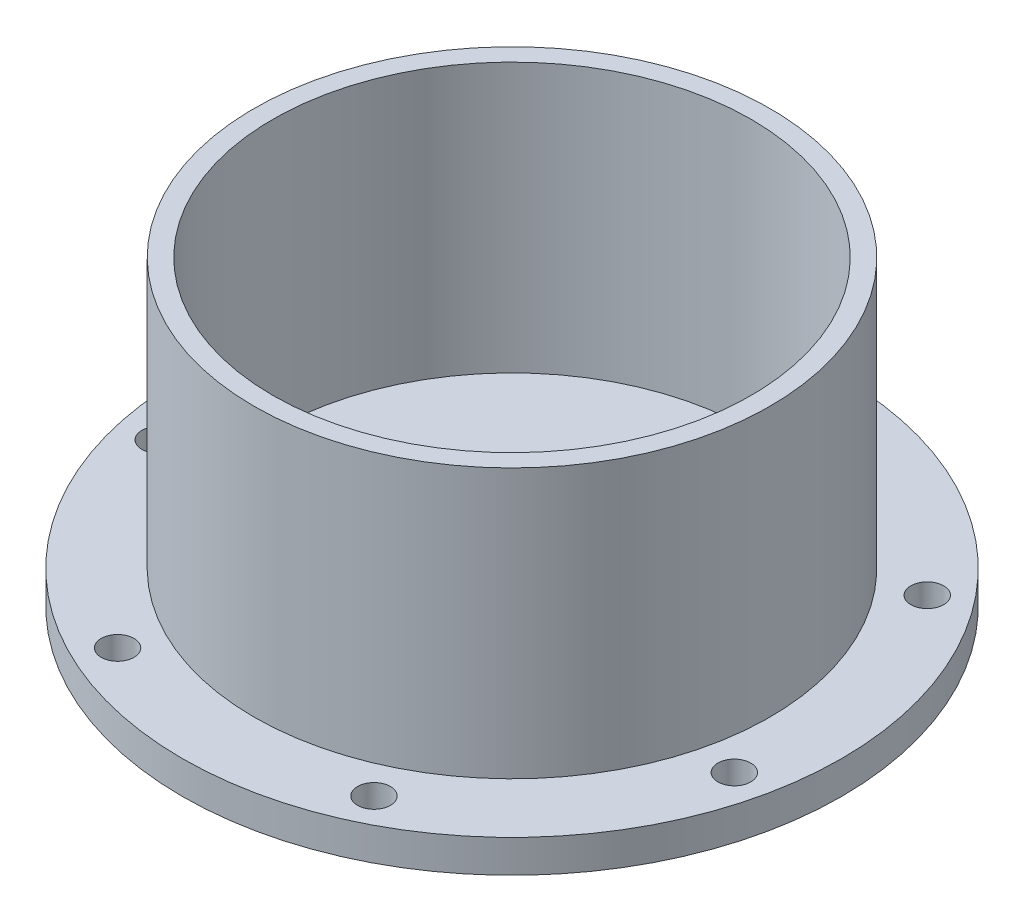
SolidWorks part; units mm, degrees
material "Cast Alloy Steel"
ref_plane "Front Plane" through (0, 0, 0) normal (0, 0, 1) x (1, 0, 0)
ref_plane "Top Plane" through (0, 0, 0) normal (0, 1, 0) x (1, 0, 0)
ref_plane "Right Plane" through (0, 0, 0) normal (1, 0, 0) x (0, 0, -1)
sketch "Sketch2" plane through (0, 0, 0) normal (0, 1, 0) x (1, 0, 0)
  line L0 (0, 0) -> (0, 31.5) construction
  circle A0 centre (0, 0) radius 35.15
  circle A1 centre (0, 31.5) radius 1.75
  circle A2 centre (24.6277, 19.6399) radius 1.75
  circle A3 centre (30.7102, -7.0094) radius 1.75
  circle A4 centre (13.6673, -28.3805) radius 1.75
  circle A5 centre (-13.6673, -28.3805) radius 1.75
  circle A6 centre (-30.7102, -7.0094) radius 1.75
  circle A7 centre (-24.6277, 19.6399) radius 1.75
  point P20 (0, 0)
  dimension "D1" = 70.3
  dimension "D3" = 3.5
  dimension "D2" = 31.5
  dimension "D4" = 7
extrude "Boss-Extrude1" add sketch "Sketch2" along normal blind 3.5
sketch "Sketch3" plane through (0, 3.5, 0) normal (0, 1, 0) x (1, 0, 0)
  circle A0 centre (0, 0) radius 27.5
  circle A1 centre (0, 0) radius 25.5
  dimension "D1" = 55
extrude "Boss-Extrude2" add sketch "Sketch3" along normal blind 28.7
